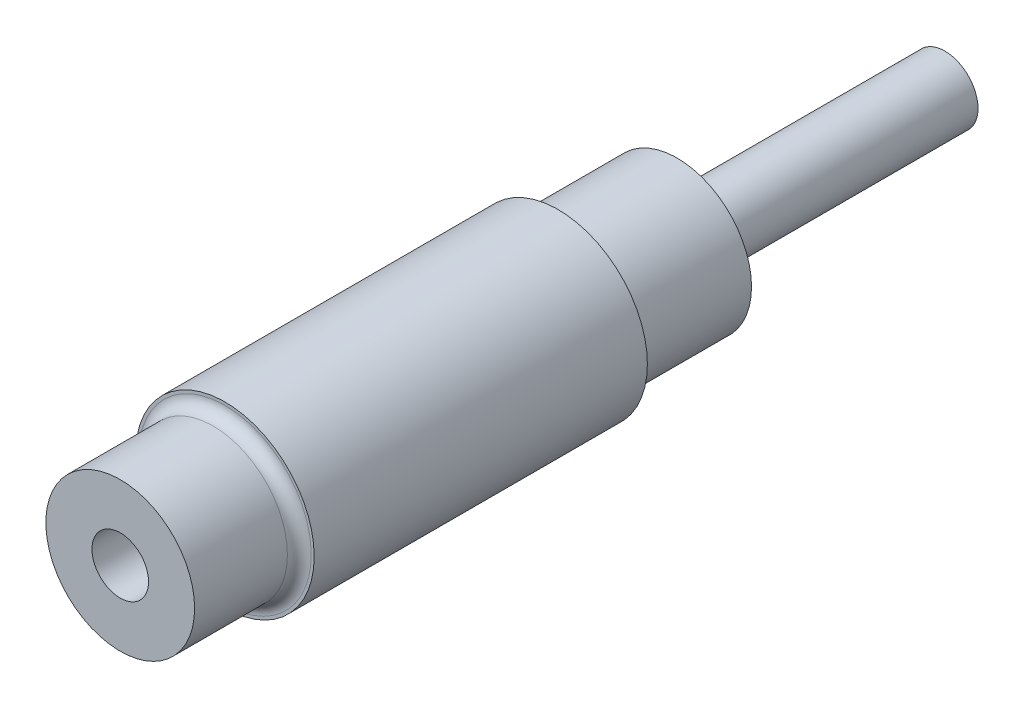
SolidWorks part; units mm, degrees
ref_plane "Front Plane" through (0, 0, 0) normal (0, 0, 1) x (1, 0, 0)
ref_plane "Top Plane" through (0, 0, 0) normal (0, 1, 0) x (1, 0, 0)
ref_plane "Right Plane" through (0, 0, 0) normal (1, 0, 0) x (0, 0, -1)
sketch "Sketch1" plane through (0, 0, 0) normal (0, 0, 1) x (1, 0, 0)
  circle A0 centre (0, 0) radius 12.5
  dimension "D1" = 25
extrude "Boss-Extrude1" add sketch "Sketch1" along normal blind 93.6
ref_plane "Plane1" through (0, 0, 76) normal (0, 0, 1) x (1, 0, 0)
sketch "Sketch2" plane through (0, 0, 76) normal (0, 0, 1) x (1, 0, 0)
  circle A0 centre (0, 0) radius 15
  dimension "D1" = 30
extrude "Boss-Extrude2" add sketch "Sketch2" against normal blind 56
sketch "Sketch3" plane through (0, 0, 0) normal (0, 0, -1) x (-1, 0, 0)
  circle A0 centre (0, 0) radius 5.565
  dimension "D1" = 11.13
extrude "Boss-Extrude3" add sketch "Sketch3" along normal blind 45
sketch "Sketch4" plane through (0, 0, 93.6) normal (0, 0, 1) x (1, 0, 0)
  circle A0 centre (0, 0) radius 4.755
  dimension "D1" = 9.51
extrude "Cut-Extrude1" cut sketch "Sketch4" against normal blind 60
fillet "Fillet2" radius 2 1 edges at (12.5, 0, 76)
fillet "Fillet3" radius 1.5 1 edges at (12.5, 0, 20)
fillet "Fillet4" radius 2 1 edges at (-5.565, 0, 0)
